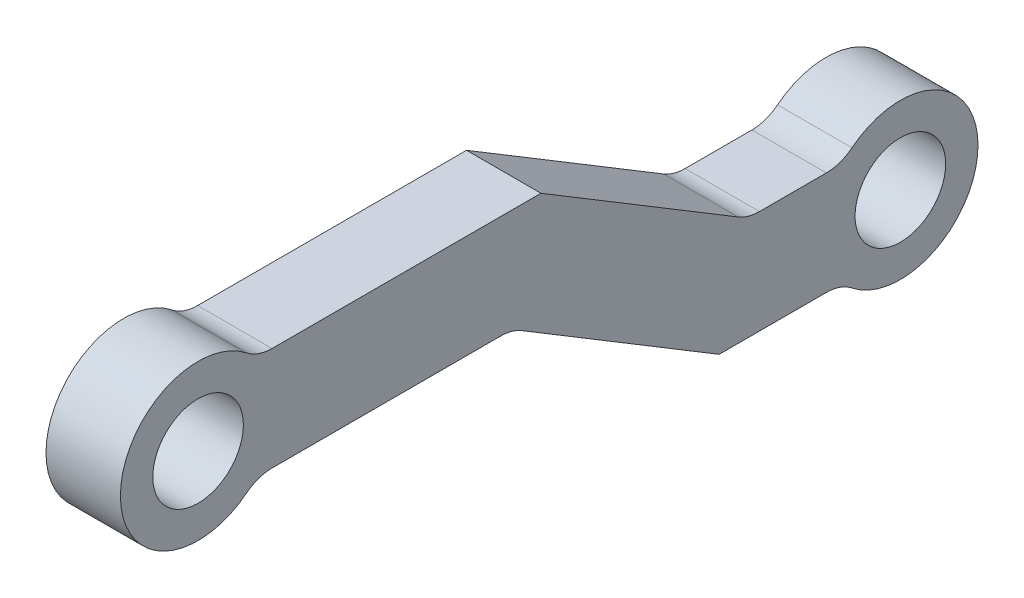
SolidWorks part; units mm, degrees
material "Plain Carbon Steel"
ref_plane "Front Plane" through (0, 0, 0) normal (0, 0, 1) x (1, 0, 0)
ref_plane "Top Plane" through (0, 0, 0) normal (0, 1, 0) x (1, 0, 0)
ref_plane "Right Plane" through (0, 0, 0) normal (1, 0, 0) x (0, 0, -1)
sketch "Sketch2" plane through (0, 0, 0) normal (1, 0, 0) x (0, 0, -1)
  line L16 (2.2361, 2) -> (13.2474, 2)
  line L17 (13.2474, 2) -> (21.2474, -2.8331)
  line L18 (21.2474, -2.8331) -> (24.8968, -2.8331)
  line L19 (0, 0) -> (27.1329, -4.8331) construction
  line L26 (2.2361, -2) -> (12.1329, -2)
  line L27 (12.1329, -2) -> (20.1329, -6.8331)
  line L28 (20.1329, -6.8331) -> (24.8968, -6.8331)
  line L29 (7.7417, 2) -> (7.7417, -2) construction
  line L30 (23.0721, -2.8331) -> (23.0721, -6.8331) construction
  circle A8 centre (0, 0) radius 1.75
  circle A9 centre (27.1329, -4.8331) radius 1.75
  circle A12 centre (0, 0) radius 3
  circle A13 centre (27.1329, -4.8331) radius 3
  point P9 (23.0721, -4.8331)
  point P14 (7.7417, 0)
  dimension "D1" = 10.1
  dimension "D5" = 3.5
  dimension "D7" = 4
  dimension "D8" = 7
  dimension "D3" = 6
  dimension "D4" = 4
  dimension "D2" = 27.56
  dimension "D6" = 4
  dimension "D9" = 15
extrude "Boss-Extrude1" add sketch "Sketch2" along normal blind 2.875 contours A13 L18 L17 L16 A12 L26 L27 L28 | A8 | A9
fillet "Fillet1" radius 1.5875 6 edges at (1.4375, -6.8331, -24.8968) (1.4375, -2.8331, -21.2474) (1.4375, -2, -12.1329) (1.4375, -2, -2.2361) (1.4375, -2.8331, -24.8968) (1.4375, 2, -2.2361)
